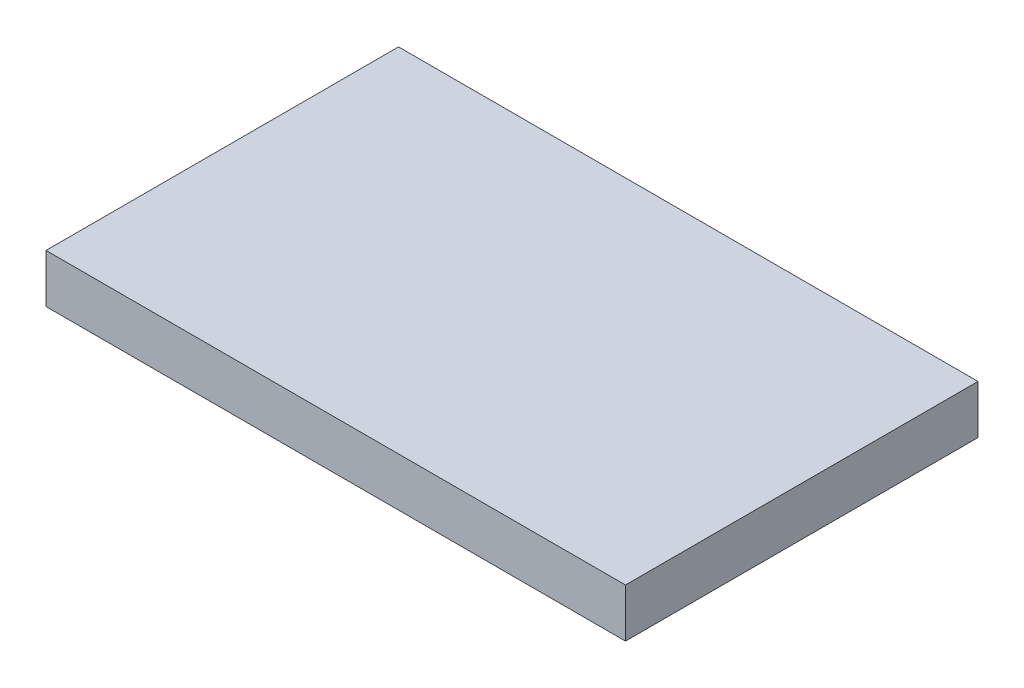
SolidWorks part; units mm, degrees
ref_plane "Front Plane" through (0, 0, 0) normal (0, 0, 1) x (1, 0, 0)
ref_plane "Top Plane" through (0, 0, 0) normal (0, 1, 0) x (1, 0, 0)
ref_plane "Right Plane" through (0, 0, 0) normal (1, 0, 0) x (0, 0, -1)
sketch "Sketch1" plane through (0, 0, 0) normal (0, 1, 0) x (1, 0, 0)
  line L0 (-18.3792, 51.3989) -> (-18.3792, -35.6011)
  line L1 (-18.3792, -35.6011) -> (124.6208, -35.6011)
  line L2 (124.6208, -35.6011) -> (124.6208, 51.3989)
  line L3 (124.6208, 51.3989) -> (-18.3792, 51.3989)
  dimension "D1" = 143
  dimension "D2" = 87
extrude "Boss-Extrude1" add sketch "Sketch1" along normal blind 12
